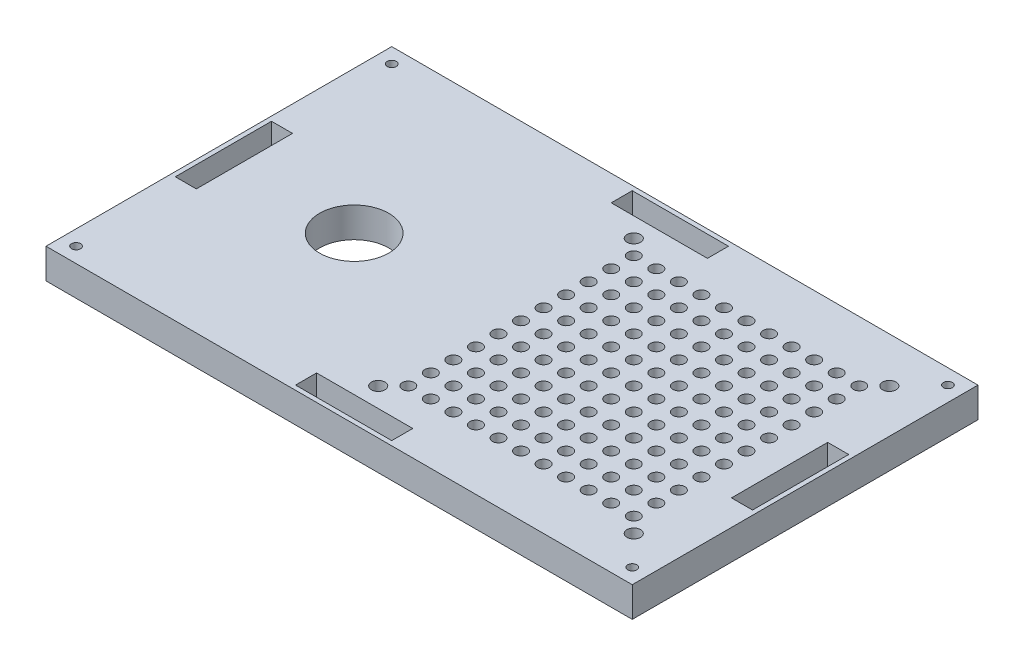
SolidWorks part; units mm, degrees
ref_plane "Plano frontal" through (0, 0, 0) normal (0, 0, 1) x (1, 0, 0)
ref_plane "Plano superior" through (0, 0, 0) normal (0, 1, 0) x (1, 0, 0)
ref_plane "Plano direito" through (0, 0, 0) normal (1, 0, 0) x (0, 0, -1)
sketch "Esboço1" plane through (0, 0, 0) normal (0, 1, 0) x (1, 0, 0)
  line L1 (97.5, -57.5) -> (-97.5, -57.5)
  line L2 (97.5, -57.5) -> (97.5, 57.5)
  line L3 (97.5, 57.5) -> (-97.5, 57.5)
  line L4 (-97.5, -57.5) -> (-97.5, 57.5)
  line L5 (97.5, -57.5) -> (-97.5, 57.5) construction
  line L6 (97.5, 57.5) -> (-97.5, -57.5) construction
  point P0 (0, 0)
  dimension "D1" = 195
  dimension "D2" = 115
extrude "Ressalto-extrusão1" add sketch "Esboço1" along normal blind 10
sketch "Esboço2" plane through (0, 10, 0) normal (0, 1, 0) x (1, 0, 0)
  line L0 (0, -86.5716) -> (0, 73.7054) construction
  line L1 (-137.4853, 0) -> (143.3671, 0) construction
  line L7 (-97.5, 57.5) -> (-97.5, -57.5) construction
  line L8 (-89, -16) -> (-96, -16)
  line L27 (-89, -16) -> (-89, 16)
  line L28 (-89, 16) -> (-96, 16)
  line L41 (-96, -16) -> (-96, 16)
  line L42 (-89, -16) -> (-96, 16) construction
  line L43 (-89, 16) -> (-96, -16) construction
  line L44 (-97.5, -57.5) -> (97.5, -57.5) construction
  line L45 (16, -56) -> (-16, -56)
  line L46 (16, -56) -> (16, -49)
  line L47 (16, -49) -> (-16, -49)
  line L48 (-16, -56) -> (-16, -49)
  line L49 (16, -56) -> (-16, -49) construction
  line L50 (16, -49) -> (-16, -56) construction
  line L51 (89, -16) -> (96, -16)
  line L52 (89, -16) -> (89, 16)
  line L53 (96, -16) -> (96, 16)
  line L54 (89, 16) -> (96, 16)
  line L55 (16, 56) -> (16, 49)
  line L56 (16, 56) -> (-16, 56)
  line L57 (-16, 56) -> (-16, 49)
  line L58 (16, 49) -> (-16, 49)
  line L59 (97.5, 57.5) -> (-97.5, 57.5) construction
  circle A0 centre (-92.5, 52.5) radius 1.5
  circle A1 centre (92.5, 52.5) radius 1.5
  circle A3 centre (92.5, -52.5) radius 1.5
  circle A4 centre (-92.5, -52.5) radius 1.5
  point P5 (-92.5, 0)
  point P12 (0, -52.5)
  point P33 (92.5, -52.5)
  dimension "D7" = 3
  dimension "D8" = 5
  dimension "D9" = 5
  dimension "D1" = 32
  dimension "D2" = 7
  dimension "D3" = 1.5
  dimension "D4" = 32
  dimension "D5" = 7
  dimension "D6" = 1.5
extrude "Corte-extrusão2" cut sketch "Esboço2" against normal through all
sketch "Esboço3" plane through (0, 10, 0) normal (0, 1, 0) x (1, 0, 0)
  line L0 (-123.9213, 0) -> (127.074, 0) construction
  line L1 (0, -71.5978) -> (0, 79.4131) construction
  line L3 (97.5, -57.5) -> (97.5, 57.5) construction
  line L4 (83, -42.5) -> (-2, -42.5) construction
  line L5 (83, -42.5) -> (83, 42.5) construction
  line L6 (83, 42.5) -> (-2, 42.5) construction
  line L7 (-2, -42.5) -> (-2, 42.5) construction
  line L8 (83, -42.5) -> (-2, 42.5) construction
  line L9 (83, 42.5) -> (-2, -42.5) construction
  line L10 (53, 52.5635) -> (53, -62.2155) construction
  line L11 (78, -37.5) -> (3, -37.5) construction
  line L12 (78, -37.5) -> (78, 37.5) construction
  line L13 (78, 37.5) -> (3, 37.5) construction
  line L14 (3, -37.5) -> (3, 37.5) construction
  line L15 (78, -37.5) -> (3, 37.5) construction
  line L16 (78, 37.5) -> (3, -37.5) construction
  line L17 (-97.5, 57.5) -> (-97.5, -57.5) construction
  line L18 (-97.5, -57.5) -> (97.5, -57.5) construction
  circle A1 centre (83, 42.5) radius 2.25
  circle A2 centre (83, -42.5) radius 2.25
  circle A3 centre (-2, -42.5) radius 2.25
  circle A4 centre (-2, 42.5) radius 2.25
  circle A13 centre (3, 37.5) radius 2
  circle A14 centre (10.5, 37.5) radius 2
  circle A15 centre (18, 37.5) radius 2
  circle A16 centre (25.5, 37.5) radius 2
  circle A17 centre (33, 37.5) radius 2
  circle A18 centre (40.5, 37.5) radius 2
  circle A19 centre (48, 37.5) radius 2
  circle A20 centre (55.5, 37.5) radius 2
  circle A21 centre (63, 37.5) radius 2
  circle A22 centre (70.5, 37.5) radius 2
  circle A23 centre (78, 37.5) radius 2
  circle A24 centre (10.5, 30) radius 2
  circle A25 centre (18, 30) radius 2
  circle A26 centre (25.5, 30) radius 2
  circle A27 centre (33, 30) radius 2
  circle A28 centre (40.5, 30) radius 2
  circle A29 centre (48, 30) radius 2
  circle A30 centre (55.5, 30) radius 2
  circle A31 centre (63, 30) radius 2
  circle A32 centre (70.5, 30) radius 2
  circle A33 centre (78, 30) radius 2
  circle A34 centre (10.5, 22.5) radius 2
  circle A35 centre (18, 22.5) radius 2
  circle A36 centre (25.5, 22.5) radius 2
  circle A37 centre (33, 22.5) radius 2
  circle A38 centre (40.5, 22.5) radius 2
  circle A39 centre (48, 22.5) radius 2
  circle A40 centre (55.5, 22.5) radius 2
  circle A41 centre (63, 22.5) radius 2
  circle A42 centre (70.5, 22.5) radius 2
  circle A43 centre (78, 22.5) radius 2
  circle A44 centre (10.5, 15) radius 2
  circle A45 centre (18, 15) radius 2
  circle A46 centre (25.5, 15) radius 2
  circle A47 centre (33, 15) radius 2
  circle A48 centre (40.5, 15) radius 2
  circle A49 centre (48, 15) radius 2
  circle A50 centre (55.5, 15) radius 2
  circle A51 centre (63, 15) radius 2
  circle A52 centre (70.5, 15) radius 2
  circle A53 centre (78, 15) radius 2
  circle A54 centre (10.5, 7.5) radius 2
  circle A55 centre (18, 7.5) radius 2
  circle A56 centre (25.5, 7.5) radius 2
  circle A57 centre (33, 7.5) radius 2
  circle A58 centre (40.5, 7.5) radius 2
  circle A59 centre (48, 7.5) radius 2
  circle A60 centre (55.5, 7.5) radius 2
  circle A61 centre (63, 7.5) radius 2
  circle A62 centre (70.5, 7.5) radius 2
  circle A63 centre (78, 7.5) radius 2
  circle A64 centre (10.5, 0) radius 2
  circle A65 centre (18, 0) radius 2
  circle A66 centre (25.5, 0) radius 2
  circle A67 centre (33, 0) radius 2
  circle A68 centre (40.5, 0) radius 2
  circle A69 centre (48, 0) radius 2
  circle A70 centre (55.5, 0) radius 2
  circle A71 centre (63, 0) radius 2
  circle A72 centre (70.5, 0) radius 2
  circle A73 centre (78, 0) radius 2
  circle A74 centre (10.5, -7.5) radius 2
  circle A75 centre (18, -7.5) radius 2
  circle A76 centre (25.5, -7.5) radius 2
  circle A77 centre (33, -7.5) radius 2
  circle A78 centre (40.5, -7.5) radius 2
  circle A79 centre (48, -7.5) radius 2
  circle A80 centre (55.5, -7.5) radius 2
  circle A81 centre (63, -7.5) radius 2
  circle A82 centre (70.5, -7.5) radius 2
  circle A83 centre (78, -7.5) radius 2
  circle A84 centre (10.5, -15) radius 2
  circle A85 centre (18, -15) radius 2
  circle A86 centre (25.5, -15) radius 2
  circle A87 centre (33, -15) radius 2
  circle A88 centre (40.5, -15) radius 2
  circle A89 centre (48, -15) radius 2
  circle A90 centre (55.5, -15) radius 2
  circle A91 centre (63, -15) radius 2
  circle A92 centre (70.5, -15) radius 2
  circle A93 centre (78, -15) radius 2
  circle A94 centre (10.5, -22.5) radius 2
  circle A95 centre (18, -22.5) radius 2
  circle A96 centre (25.5, -22.5) radius 2
  circle A97 centre (33, -22.5) radius 2
  circle A98 centre (40.5, -22.5) radius 2
  circle A99 centre (48, -22.5) radius 2
  circle A100 centre (55.5, -22.5) radius 2
  circle A101 centre (63, -22.5) radius 2
  circle A102 centre (70.5, -22.5) radius 2
  circle A103 centre (78, -22.5) radius 2
  circle A104 centre (10.5, -30) radius 2
  circle A105 centre (18, -30) radius 2
  circle A106 centre (25.5, -30) radius 2
  circle A107 centre (33, -30) radius 2
  circle A108 centre (40.5, -30) radius 2
  circle A109 centre (48, -30) radius 2
  circle A110 centre (55.5, -30) radius 2
  circle A111 centre (63, -30) radius 2
  circle A112 centre (70.5, -30) radius 2
  circle A113 centre (78, -30) radius 2
  circle A114 centre (10.5, -37.5) radius 2
  circle A115 centre (18, -37.5) radius 2
  circle A116 centre (25.5, -37.5) radius 2
  circle A117 centre (33, -37.5) radius 2
  circle A118 centre (40.5, -37.5) radius 2
  circle A119 centre (48, -37.5) radius 2
  circle A120 centre (55.5, -37.5) radius 2
  circle A121 centre (63, -37.5) radius 2
  circle A122 centre (70.5, -37.5) radius 2
  circle A123 centre (78, -37.5) radius 2
  circle A124 centre (3, 30) radius 2
  circle A125 centre (3, 22.5) radius 2
  circle A126 centre (3, 15) radius 2
  circle A127 centre (3, 7.5) radius 2
  circle A128 centre (3, 0) radius 2
  circle A129 centre (3, -7.5) radius 2
  circle A130 centre (3, -15) radius 2
  circle A131 centre (3, -22.5) radius 2
  circle A132 centre (3, -30) radius 2
  circle A133 centre (3, -37.5) radius 2
  circle A134 centre (-50, -2.5) radius 11.5
  point P9 (40.5, 0)
  point P16 (40.5, 0)
  dimension "D2" = 4.5
  dimension "D5" = 75
  dimension "D6" = 75
  dimension "D7" = 4
  dimension "D9" = 23
  dimension "D10" = 55
  dimension "D11" = 47.5
  dimension "D1" = 57
  dimension "D3" = 85
  dimension "D4" = 85
  dimension "D8" = 11
extrude "Corte-extrusão3" cut sketch "Esboço3" against normal through all
